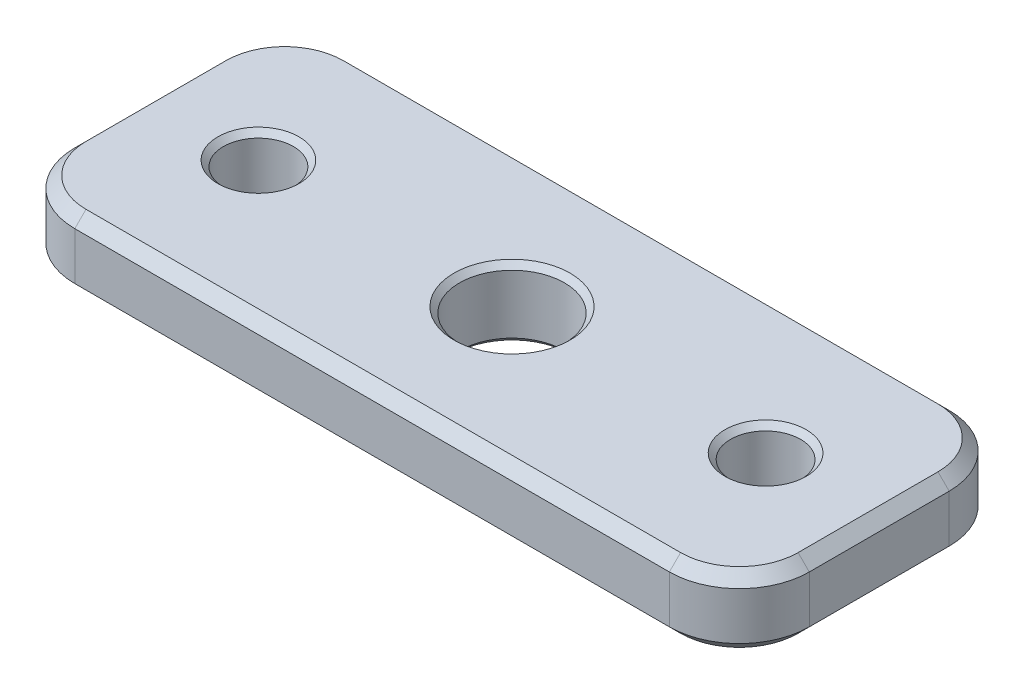
SolidWorks part; units mm, degrees
ref_plane "Front" through (0, 0, 0) normal (0, 0, 1) x (1, 0, 0)
ref_plane "Top" through (0, 0, 0) normal (0, 1, 0) x (1, 0, 0)
ref_plane "Right" through (0, 0, 0) normal (1, 0, 0) x (0, 0, -1)
sketch "Sketch1" plane through (0, 0, 0) normal (0, 1, 0) x (1, 0, 0)
  line L0 (11.5094, 0) -> (0, 0) construction
  line L1 (-16.6687, -6.35) -> (16.6688, -6.35)
  line L2 (-16.6687, -6.35) -> (-16.6687, 6.35)
  line L3 (-16.6687, 6.35) -> (16.6688, 6.35)
  line L4 (16.6688, -6.35) -> (16.6688, 6.35)
  line L5 (-16.6687, -6.35) -> (16.6688, 6.35) construction
  line L6 (-16.6687, 6.35) -> (16.6688, -6.35) construction
  line L7 (0, 0) -> (-11.5094, 0) construction
  circle A0 centre (-11.5094, 0) radius 1.5875
  circle A1 centre (11.5094, 0) radius 1.5875
  circle A2 centre (0, 0) radius 2.3813
  point P0 (0, 0)
  dimension "D4" = 3.175
  dimension "D5" = 4.7625
  dimension "D1" = 12.7
  dimension "D2" = 33.3375
  dimension "D3" = 11.5094
extrude "Boss-Extrude1" add sketch "Sketch1" along normal blind 3.175
fillet "Fillet1" radius 3.175 4 edges at (16.6688, 1.5875, 6.35) (-16.6687, 1.5875, -6.35) (16.6688, 1.5875, -6.35) (-16.6687, 1.5875, 6.35)
chamfer "Chamfer2" distance 0.508 angle 45 16 edges at (0, 3.175, -6.35) (-15.7388, 3.175, -5.4201) (15.7388, 3.175, -5.4201) (-16.6687, 3.175, 0) (16.6688, 3.175, 0) (-15.7388, 3.175, 5.4201) (15.7388, 3.175, 5.4201) (0, 3.175, 6.35) (0, 0, -6.35) (-15.7388, 0, -5.4201) (15.7388, 0, -5.4201) (-16.6687, 0, 0) (16.6688, 0, 0) (-15.7388, 0, 5.4201) (15.7388, 0, 5.4201) (0, 0, 6.35)
chamfer "Chamfer1" distance 0.254 angle 45 6 edges at (0, 0, 2.3813) (-11.5094, 0, 1.5875) (11.5094, 0, 1.5875) (0, 3.175, 2.3813) (11.5094, 3.175, 1.5875) (-11.5094, 3.175, 1.5875)
